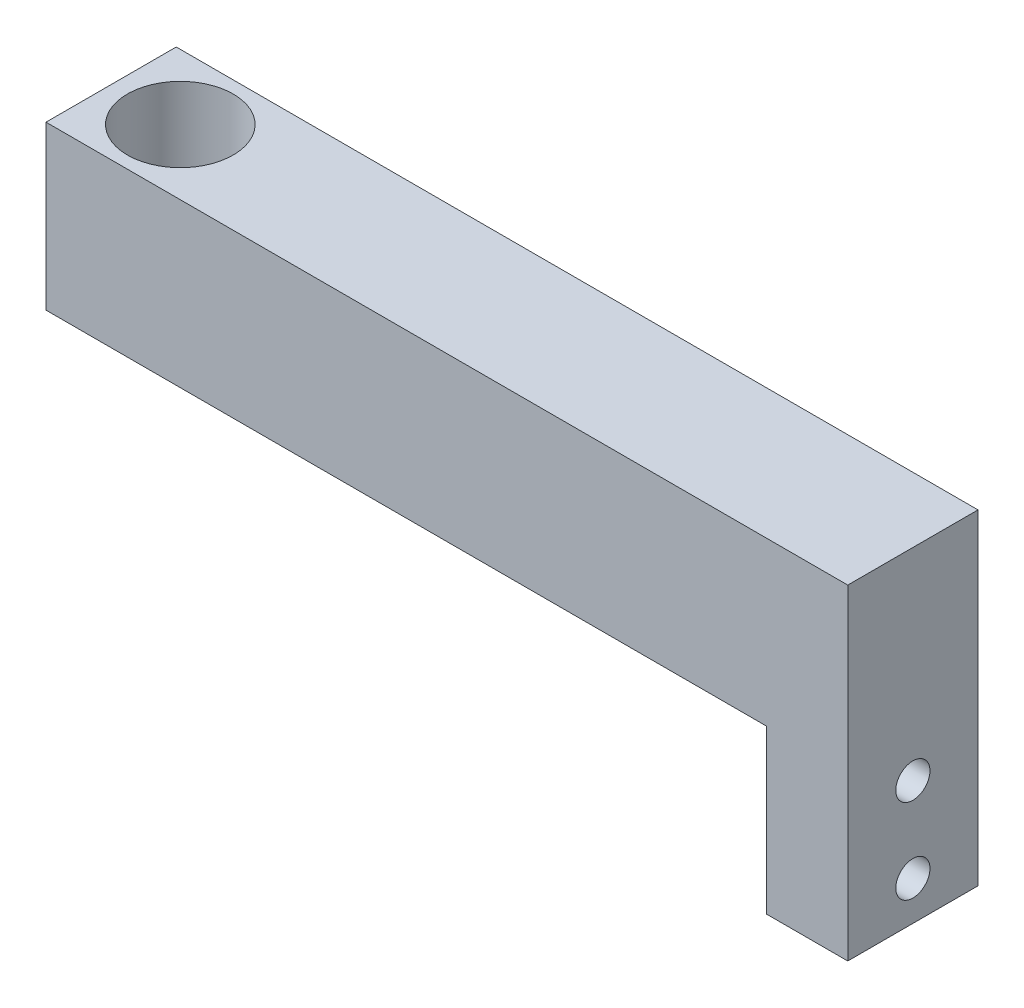
SolidWorks part; units mm, degrees
ref_plane "前视基准面" through (0, 0, 0) normal (0, 0, 1) x (1, 0, 0)
ref_plane "上视基准面" through (0, 0, 0) normal (0, 1, 0) x (1, 0, 0)
ref_plane "右视基准面" through (0, 0, 0) normal (1, 0, 0) x (0, 0, -1)
other "Configuration Table"
sketch "草图1" plane through (0, 0, 0) normal (0, 1, 0) x (1, 0, 0)
  line L1 (-8.5, 8) -> (80, 8)
  line L2 (-8.5, 8) -> (-8.5, -8)
  line L3 (-8.5, -8) -> (80, -8)
  line L4 (80, 8) -> (80, -8)
  circle A0 centre (0, 0) radius 6.5
  dimension "D1" = 13
  dimension "D2" = 8
  dimension "D3" = 8
  dimension "D4" = 8.5
  dimension "D5" = 80
extrude "凸台-拉伸1" add sketch "草图1" along normal blind 20
sketch "草图2" plane through (80, 0, 0) normal (1, 0, 0) x (0, 0, -1)
  line L1 (-8, 20) -> (8, 20)
  line L2 (-8, 20) -> (-8, -20)
  line L3 (-8, -20) -> (8, -20)
  line L4 (8, 20) -> (8, -20)
  dimension "D1" = 16
  dimension "D2" = 40
extrude "凸台-拉伸2" add sketch "草图2" along normal blind 10
sketch "草图3" plane through (80, 0, 0) normal (-1, 0, 0) x (0, 0, 1)
  line L0 (-8, -20) -> (-8, 0) construction
  line L1 (8, -20) -> (-8, -20) construction
  line L2 (8, 0) -> (-8, 0) construction
  circle A0 centre (0, -4.8) radius 2.1
  circle A1 centre (0, -15.2) radius 2.1
  dimension "D4" = 4.2
  dimension "D5" = 4.2
  dimension "D1" = 8
  dimension "D2" = 4.8
  dimension "D3" = 4.8
  dimension "D6" = 8
extrude "切除-拉伸1" cut sketch "草图3" against normal blind 10
